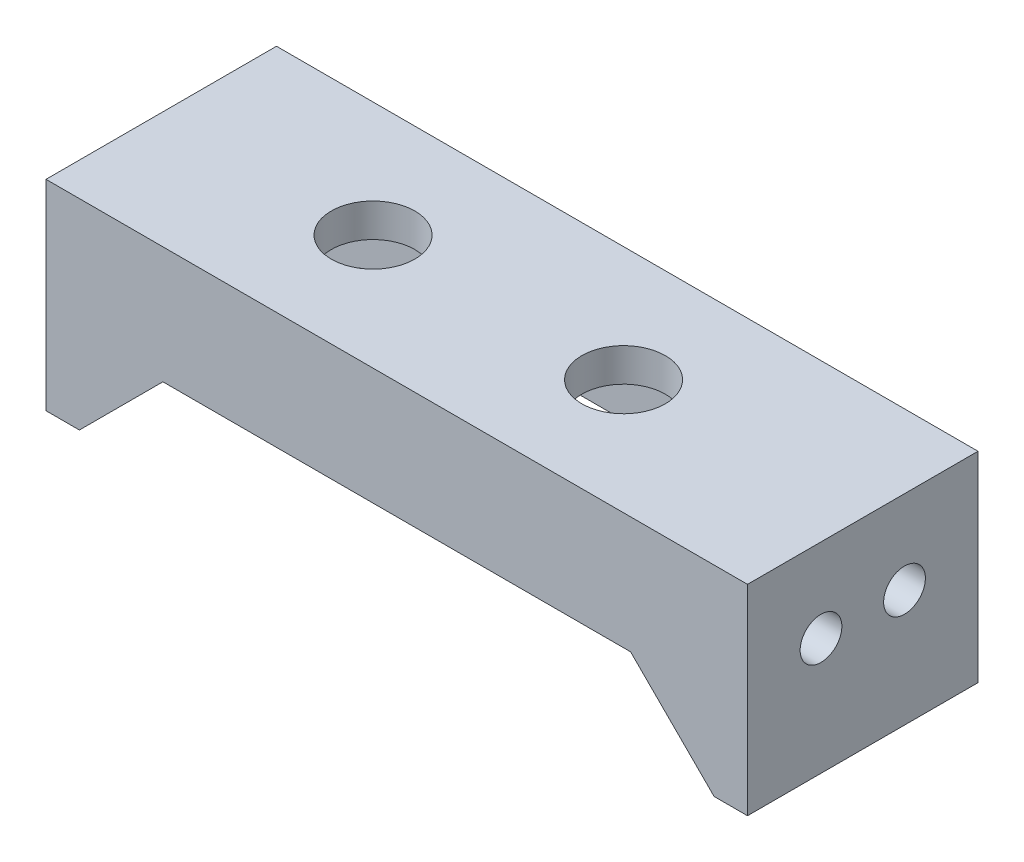
SolidWorks part; units mm, degrees
ref_plane "Front Plane" through (0, 0, 0) normal (0, 0, 1) x (1, 0, 0)
ref_plane "Top Plane" through (0, 0, 0) normal (0, 1, 0) x (1, 0, 0)
ref_plane "Right Plane" through (0, 0, 0) normal (1, 0, 0) x (0, 0, -1)
sketch "Sketch2" plane through (0, 0, 0) normal (0, 1, 0) x (1, 0, 0)
  line L1 (-21, 6.9) -> (21, 6.9)
  line L2 (-21, 6.9) -> (-21, -6.9)
  line L3 (-21, -6.9) -> (21, -6.9)
  line L4 (21, 6.9) -> (21, -6.9)
  line L5 (-21, 6.9) -> (21, -6.9) construction
  line L6 (-21, -6.9) -> (21, 6.9) construction
  point P0 (0, 0)
  dimension "D1" = 13.8
  dimension "D2" = 42
extrude "Boss-Extrude1" add sketch "Sketch2" along normal blind 2
sketch "Sketch3" plane through (0, 0, 0) normal (0, -1, 0) x (1, 0, 0)
  line L0 (21, -6.9) -> (-21, -6.9) construction
  line L1 (-21, 6.9) -> (-19, 6.9)
  line L2 (-21, 6.9) -> (-21, -6.9)
  line L3 (-21, -6.9) -> (-19, -6.9)
  line L4 (-19, 6.9) -> (-19, -6.9)
  line L5 (-21, 6.9) -> (21, 6.9) construction
  line L6 (21, 6.9) -> (19, 6.9)
  line L7 (21, 6.9) -> (21, -6.9)
  line L8 (21, -6.9) -> (19, -6.9)
  line L9 (19, 6.9) -> (19, -6.9)
  line L10 (21, 6.9) -> (21, -6.9) construction
  dimension "D1" = 2
  dimension "D2" = 2
extrude "Boss-Extrude2" add sketch "Sketch3" along normal blind 10
sketch "Sketch4" plane through (0, 0, 6.9) normal (0, 0, 1) x (1, 0, 0)
  line L5 (0, 2) -> (0, 0) construction
  line L6 (-21, 2) -> (21, 2) construction
  line L10 (-19, 0) -> (19, 0) construction
  line L11 (-19, 0) -> (19, 0)
  line L12 (-19, -10) -> (-19, 0) construction
  line L13 (-19, -10) -> (-19, 0)
  line L14 (19, -10) -> (19, 0) construction
  line L15 (19, -10) -> (19, 0)
  line L16 (-14, -5) -> (14, -5)
  line L17 (-19, -10) -> (-14, -5)
  line L18 (19, -10) -> (14, -5)
extrude "Boss-Extrude3" add sketch "Sketch4" against normal blind 2
mirror "Mirror1" about plane through (0, 0, 0) normal (0, 0, 1) of "Boss-Extrude3"
sketch "Sketch5" plane through (0, 0, 0) normal (0, -1, 0) x (1, 0, 0)
  line L0 (-19, 0) -> (19, 0) construction
  line L1 (-19, -4.9) -> (-19, 4.9) construction
  line L2 (19, 4.9) -> (19, -4.9) construction
  circle A0 centre (-8.3199, 0) radius 2.5
  circle A1 centre (6.6801, 0) radius 2.5
  dimension "D1" = 5
  dimension "D2" = 5
  dimension "D3" = 15
extrude "Cut-Extrude1" cut sketch "Sketch5" against normal blind 2
sketch "Sketch6" plane through (-19, 0, 0) normal (1, 0, 0) x (0, 0, -1)
  line L0 (4.9, -10) -> (-4.9, -10) construction
  line L1 (0, 0) -> (0, -10) construction
  line L2 (4.9, 0) -> (-4.9, 0) construction
  circle A0 centre (-2.5, -3) radius 1.25
  circle A1 centre (2.5, -3) radius 1.25
  dimension "D1" = 2.5
  dimension "D2" = 2.5
  dimension "D3" = 5
  dimension "D4" = 3
  dimension "D5" = 3
  dimension "D6" = 2.5
extrude "Cut-Extrude2" cut sketch "Sketch6" against normal blind 2
mirror "Mirror2" about plane through (0, 0, 0) normal (1, 0, 0) of "Cut-Extrude2"
